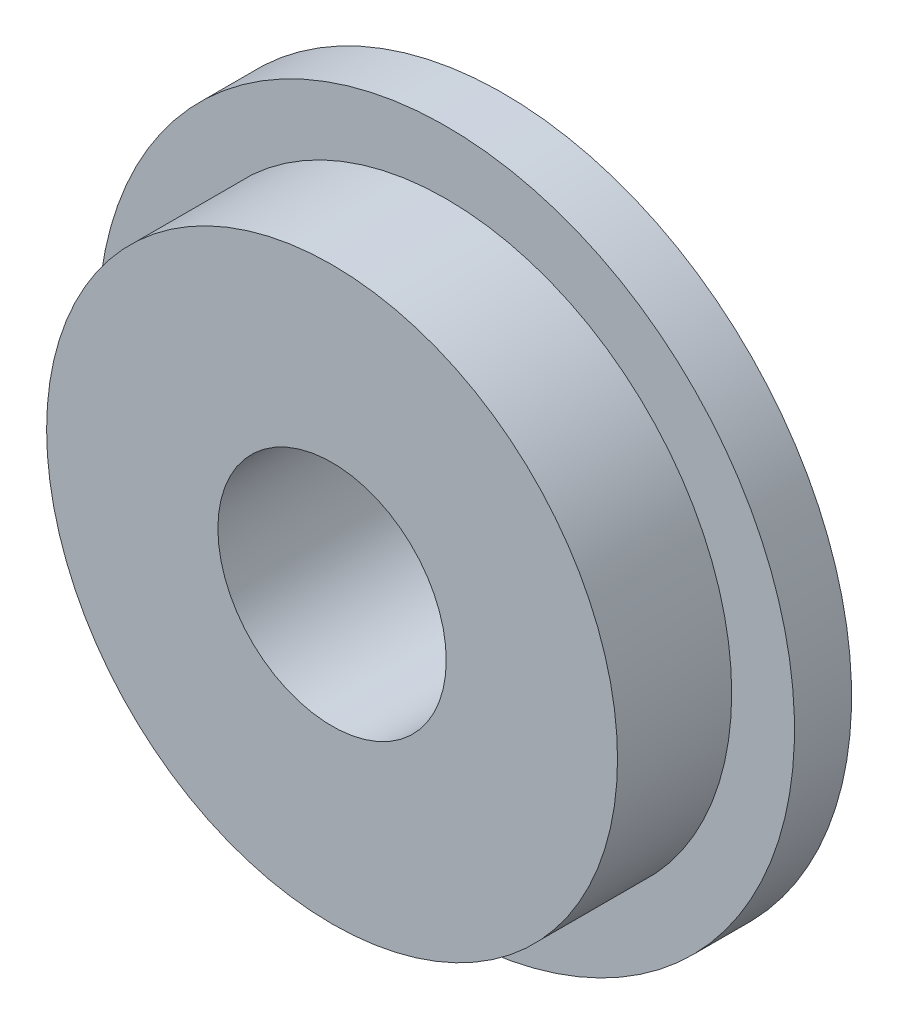
SolidWorks part; units mm, degrees
material "Сталь ШХ15 ГОСТ 801-78"
ref_plane "Plane1" through (0, 0, 0) normal (0, 0, 1) x (1, 0, 0)
ref_plane "Plane2" through (0, 0, 0) normal (0, 1, 0) x (1, 0, 0)
ref_plane "Plane3" through (0, 0, 0) normal (1, 0, 0) x (0, 0, -1)
sketch "Эскиз1" plane through (0, 0, 0) normal (0, 0, 1) x (1, 0, 0)
  circle A0 centre (0, 0) radius 2.5
  dimension "D1" = 5
extrude "Бобышка-Вытянуть1" add sketch "Эскиз1" along normal blind 1.5 contours A0
sketch "Эскиз3" plane through (0, 0, 0) normal (0, 0, -1) x (-1, 0, 0)
  circle A0 centre (0, 0) radius 3.05
  dimension "D1" = 6.1
extrude "Бобышка-Вытянуть2" add sketch "Эскиз3" against normal blind 0.5
sketch "Эскиз4" plane through (0, 0, 1.5) normal (0, 0, 1) x (1, 0, 0)
  circle A0 centre (0, 0) radius 1
  dimension "D1" = 2
extrude "Вырез-Вытянуть1" cut sketch "Эскиз4" against normal through all both and the other way through all
